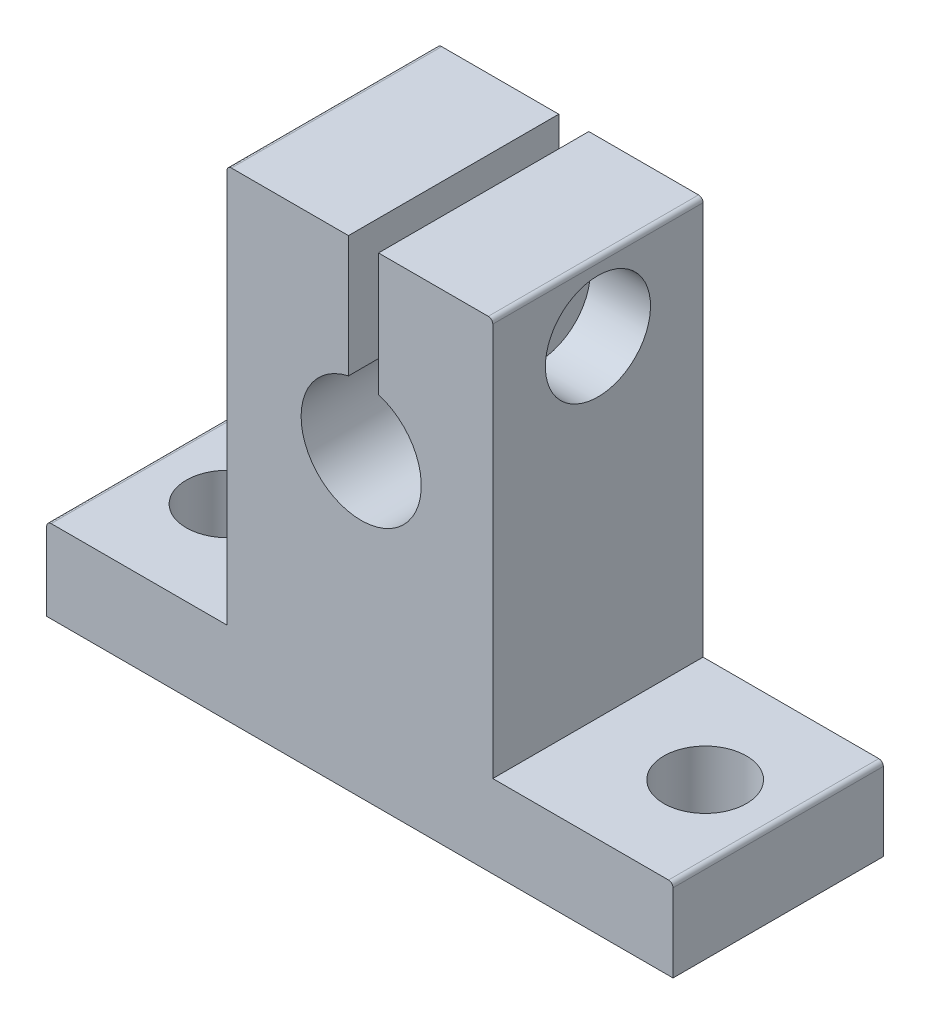
SolidWorks part; units mm, degrees
ref_plane "Front Plane" through (0, 0, 0) normal (0, 0, 1) x (1, 0, 0)
ref_plane "Top Plane" through (0, 0, 0) normal (0, 1, 0) x (1, 0, 0)
ref_plane "Right Plane" through (0, 0, 0) normal (1, 0, 0) x (0, 0, -1)
sketch "Sketch1" plane through (0, 0, 0) normal (0, 0, 1) x (1, 0, 0)
  line L1 (-20.9389, 0.7864) -> (-8.9389, 0.7864)
  line L2 (-20.9389, 0.7864) -> (-20.9389, -4.7136)
  line L3 (-20.9389, -4.7136) -> (20.7611, -4.7136)
  line L4 (20.7611, 0.7864) -> (20.7611, -4.7136)
  line L7 (-8.9389, 27.2864) -> (8.7611, 27.2864)
  line L8 (-8.9389, 27.2864) -> (-8.9389, 0.7864)
  line L9 (8.7611, 0.7864) -> (20.7611, 0.7864)
  line L10 (8.7611, 27.2864) -> (8.7611, 0.7864)
  circle A0 centre (0, 15.2864) radius 4
  point P0 (0, 0)
  point P6 (0, 0)
  dimension "D7" = 8
  dimension "D1" = 32
  dimension "D2" = 41.7
  dimension "D3" = 17.7
  dimension "D4" = 12
  dimension "D5" = 5.5
  dimension "D6" = 5.5
  dimension "D8" = 20
extrude "Boss-Extrude1" add sketch "Sketch1" along normal blind 14
sketch "Sketch2" plane through (0, 0.7864, 0) normal (0, 1, 0) x (1, 0, 0)
  line L0 (20.7611, -14) -> (8.7611, -14) construction
  line L1 (-8.9389, -14) -> (-20.9389, -14) construction
  circle A0 centre (-15.9, -7) radius 2.75
  circle A1 centre (15.9, -7) radius 2.75
  point P4 (14.7611, -14)
  dimension "D1" = 5.5
  dimension "D2" = 5.5
  dimension "D3" = 7
  dimension "D4" = 7
  dimension "D5" = 31.8
  dimension "D6" = 15.9
extrude "Cut-Extrude1" cut sketch "Sketch2" against normal blind 6
sketch "Sketch3" plane through (0, 0, 14) normal (0, 0, 1) x (1, 0, 0)
  line L1 (-0.8474, 29.683) -> (1.1526, 29.683)
  line L2 (-0.8474, 29.683) -> (-0.8474, 18.0622)
  line L3 (-0.8474, 18.0622) -> (1.1526, 18.0622)
  line L4 (1.1526, 29.683) -> (1.1526, 18.0622)
  line L5 (-0.8474, 29.683) -> (1.1526, 18.0622) construction
  line L6 (-0.8474, 18.0622) -> (1.1526, 29.683) construction
  point P0 (0.1526, 23.8726)
  dimension "D1" = 2
extrude "Cut-Extrude2" cut sketch "Sketch3" against normal blind 14
sketch "Sketch4" plane through (8.7611, 0, 0) normal (1, 0, 0) x (0, 0, -1)
  line L0 (0, 0.7864) -> (0, 27.2864) construction
  line L2 (-14, 27.2864) -> (0, 27.2864) construction
  circle A0 centre (-7, 22.7864) radius 2
  dimension "D1" = 4
  dimension "D2" = 7
  dimension "D3" = 4.5
extrude "Cut-Extrude3" cut sketch "Sketch4" against normal blind 9
sketch "Sketch5" plane through (8.7611, 0, 0) normal (1, 0, 0) x (0, 0, -1)
  circle A0 centre (-7, 22.7864) radius 3.5
  dimension "D1" = 7
extrude "Cut-Extrude4" cut sketch "Sketch5" against normal blind 4
sketch "Sketch6" plane through (-8.9389, 0, 0) normal (-1, 0, 0) x (0, 0, 1)
  line L0 (14, 27.2864) -> (14, 0.7864) construction
  line L1 (14, 27.2864) -> (0, 27.2864) construction
  circle A0 centre (7, 22.7864) radius 1.85
  point P4 (7, 27.2864)
  dimension "D1" = 3.7
  dimension "D2" = 7
  dimension "D3" = 4.5
extrude "Cut-Extrude5" cut sketch "Sketch6" against normal blind 9
fillet "Fillet1" radius 0.3 4 edges at (-8.9389, 27.2864, 7) (8.7611, 27.2864, 7) (-20.9389, 0.7864, 7) (20.7611, 0.7864, 7)
